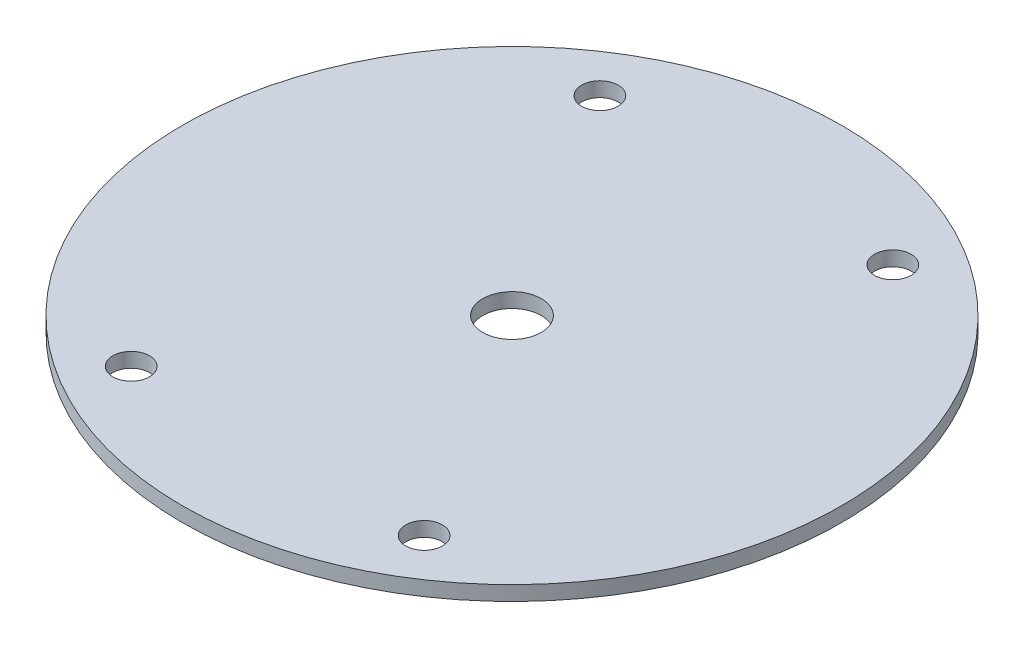
SolidWorks part; units mm, degrees
ref_plane "Front Plane" through (0, 0, 0) normal (0, 0, 1) x (1, 0, 0)
ref_plane "Top Plane" through (0, 0, 0) normal (0, 1, 0) x (1, 0, 0)
ref_plane "Right Plane" through (0, 0, 0) normal (1, 0, 0) x (0, 0, -1)
sketch "Sketch1" plane through (0, 0, 0) normal (0, 1, 0) x (1, 0, 0)
  circle A0 centre (0, 0) radius 45
  circle A1 centre (-20, 32) radius 2.5
  circle A2 centre (20, 32) radius 2.5
  circle A3 centre (20, -32) radius 2.5
  circle A4 centre (-20, -32) radius 2.5
  circle A5 centre (0, 0) radius 4
  dimension "D3" = 90
  dimension "D6" = 5
  dimension "D7" = 8
  dimension "D1" = 64
  dimension "D2" = 40
  dimension "D4" = 32
  dimension "D5" = 20
extrude "Boss-Extrude1" add sketch "Sketch1" along normal blind 2
